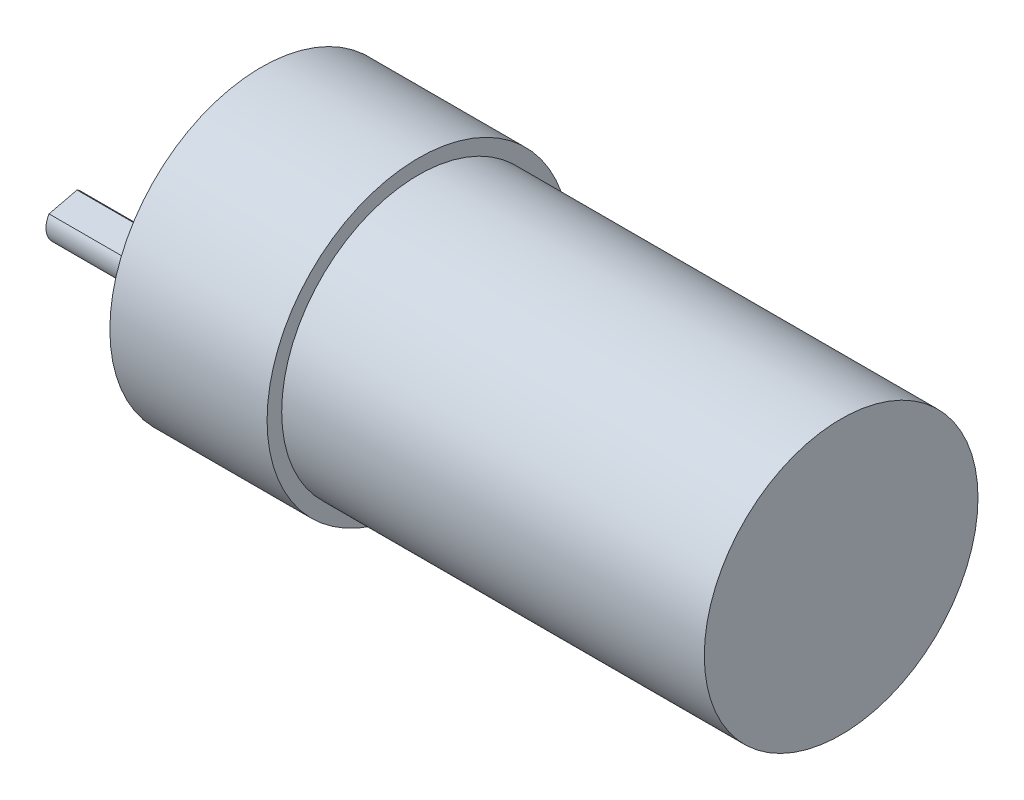
SolidWorks part; units mm, degrees
material "Steel Shell"
ref_plane "Front Plane" through (0, 0, 0) normal (0, 0, 1) x (1, 0, 0)
ref_plane "Top Plane" through (0, 0, 0) normal (0, 1, 0) x (1, 0, 0)
ref_plane "Right Plane" through (0, 0, 0) normal (1, 0, 0) x (0, 0, -1)
sketch "Sketch1" plane through (0, 0, 0) normal (1, 0, 0) x (0, 0, -1)
  circle A0 centre (0, 0) radius 15.875
  dimension "D1" = 31.75
extrude "Extrude1" add sketch "Sketch1" along normal blind 49.022
sketch "Sketch3" plane through (0, 0, 0) normal (-1, 0, 0) x (0, 0, 1)
  circle A0 centre (0, 0) radius 17.5692
extrude "Extrude3" add sketch "Sketch3" along normal blind 18.2372
sketch "Sketch4" plane through (-18.2372, 0, 0) normal (-1, 0, 0) x (0, 0, 1)
  line L0 (0, 0) -> (0, -8.7186) construction
  circle A0 centre (0, -8.7186) radius 2.3749
  dimension "D2" = 4.7498
  dimension "D1" = 8.7186
extrude "Extrude4" add sketch "Sketch4" along normal blind 22.606
sketch "Sketch5" plane through (-18.2372, 0, 0) normal (-1, 0, 0) x (0, 0, 1)
  line L0 (0, 17.5692) -> (0, 13.4556) construction
  circle A0 centre (0, 0) radius 17.5692 construction
  circle A1 centre (0, 13.4556) radius 1.27
  circle A3 centre (0, -8.7186) radius 2.3749 construction
  dimension "D2" = 2.54
  dimension "D1" = 22.1742
extrude "Cut-Extrude1" cut sketch "Sketch5" against normal blind 10
sketch "Sketch6" plane through (-18.2372, 0, 0) normal (-1, 0, 0) x (0, 0, 1)
  line L0 (0, -8.7186) -> (10.2108, -8.7186) construction
  line L1 (0, -8.7186) -> (-10.2108, -8.7186) construction
  circle A0 centre (10.2108, -8.7186) radius 1.27
  circle A4 centre (0, 13.4556) radius 1.27 construction
  circle A5 centre (-10.2108, -8.7186) radius 1.27
  circle A6 centre (0, 13.4556) radius 1.27 construction
  dimension "D1" = 10.2108
extrude "Cut-Extrude2" cut sketch "Sketch6" against normal blind 10
sketch3d "3DSketch3"
  circle A0 centre (-18.2372, -8.7186, 10.2108) radius 1.27 construction
  point P2 (-19.5072, -8.7186, 10.2108)
sketch "Sketch7" plane through (0, -5.9371, -1.4198) normal (0, 0.9726, 0.2326) x (-1, 0, 0)
  line L0 (25.8572, 1.8493) -> (18.2372, 1.8493) construction
  line L1 (25.8572, 6.9456) -> (43.5843, 6.9456)
  line L2 (25.8572, 6.9456) -> (25.8572, -4.0683)
  line L3 (25.8572, -4.0683) -> (43.5843, -4.0683)
  line L4 (43.5843, 6.9456) -> (43.5843, -4.0683)
  line L5 (18.2372, -0.3471) -> (18.2372, 4.4027) construction
  dimension "D1" = 7.62
extrude "Cut-Extrude3" cut sketch "Sketch7" against normal blind 0.6858
sketch "Sketch9" plane through (0, 0, 0) normal (1, 0, 0) x (0, 0, -1)
  line L0 (0, 0) -> (0, 15.875)
  circle A0 centre (0, 0) radius 15.875 construction
ref_plane "Plane3" through (0, 15.875, 0) normal (0, 1, 0) x (-1, 0, 0)
